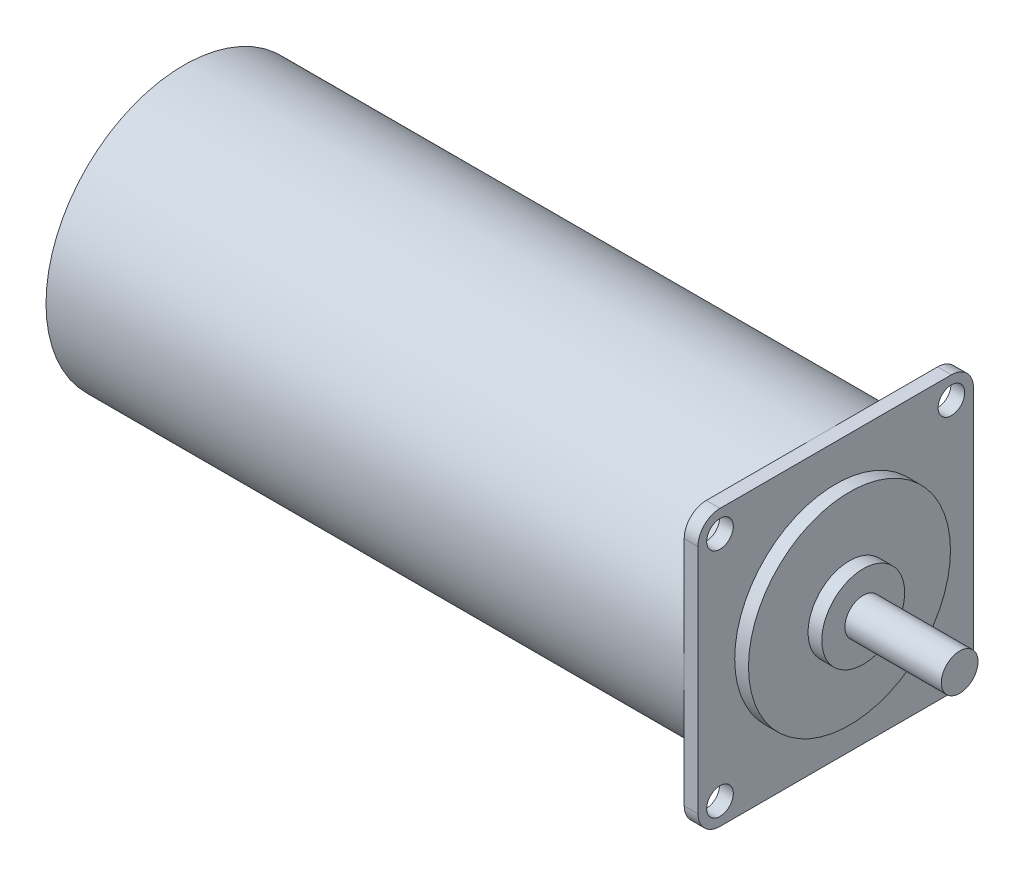
SolidWorks part; units mm, degrees
material "Сталь ШХ15 ГОСТ 801-78"
ref_plane "Plane1" through (0, 0, 0) normal (0, 0, 1) x (1, 0, 0)
ref_plane "Plane2" through (0, 0, 0) normal (0, 1, 0) x (1, 0, 0)
ref_plane "Plane3" through (0, 0, 0) normal (1, 0, 0) x (0, 0, -1)
sketch "Эскиз1" plane through (0, 0, 0) normal (0, 0, 1) x (1, 0, 0)
  line L0 (0, 0) -> (0, 15)
  line L1 (0, 15) -> (71, 15)
  line L2 (71, 15) -> (71, 11)
  line L5 (71, 11) -> (72.5, 11)
  line L6 (72.5, 11) -> (72.5, 4.5118)
  line L7 (72.5, 4.5118) -> (74, 4.5118)
  line L8 (74, 4.5118) -> (74, 2)
  line L9 (74, 2) -> (80, 2)
  line L11 (80, 2) -> (84.5, 2)
  line L12 (84.5, 2) -> (84.5, 0)
  line L13 (0, 0) -> (84.5, 0) construction
  line L14 (0, 0) -> (84.5, 0)
  dimension "D1" = 84.5
  dimension "D2" = 2
  dimension "D4" = 10.5
  dimension "D5" = 11
  dimension "D6" = 15
  dimension "D7" = 12
  dimension "D8" = 13.5
revolve "Повернуть1" add sketch "Эскиз1" angle 360 about L13
sketch "Эскиз2" plane through (71, 0, 0) normal (1, 0, 0) x (0, 0, -1)
  line L0 (15, -15) -> (15, 15)
  line L1 (15, -15) -> (-15, -15)
  line L2 (15, 15) -> (-15, 15)
  line L3 (-15, -15) -> (-15, 15)
  line L4 (0, 15) -> (0, -15) construction
  line L5 (-15, 0) -> (15, 0) construction
  circle A0 centre (0, 0) radius 15 construction
  circle A1 centre (-12.6, 12.6) radius 1.45
  circle A2 centre (12.6, 12.6) radius 1.45
  circle A3 centre (12.6, -12.6) radius 1.45
  circle A4 centre (-12.6, -12.6) radius 1.45
  point P1 (0, 0)
  dimension "D1" = 25.2
  dimension "D2" = 2.9
  dimension "D3" = 25.2
extrude "Бобышка-Вытянуть1" add sketch "Эскиз2" against normal blind 1.5
fillet "Скругление1" radius 2.4 4 edges at (70.25, -15, -15) (70.25, -15, 15) (70.25, 15, 15) (70.25, 15, -15)
